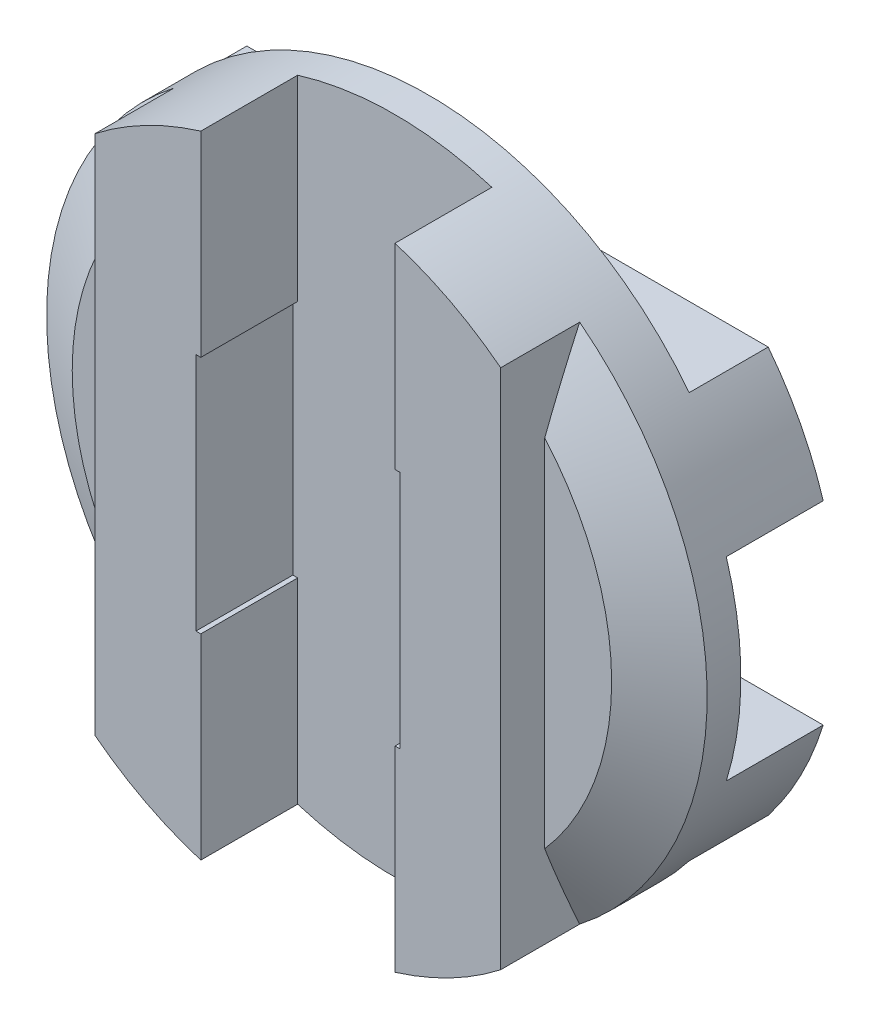
SolidWorks part; units mm, degrees
ref_plane "Front" through (0, 0, 0) normal (0, 0, 1) x (1, 0, 0)
ref_plane "Top" through (0, 0, 0) normal (0, 1, 0) x (1, 0, 0)
ref_plane "Right" through (0, 0, 0) normal (1, 0, 0) x (0, 0, -1)
sketch "Sketch1" plane through (0, 0, 0) normal (0, 0, 1) x (1, 0, 0)
  circle A0 centre (0, 0) radius 9.525
  point P3 (0, 9.525)
extrude "Boss-Extrude1" add sketch "Sketch1" against normal mid plane 6.0452
sketch "Sketch2" plane through (0, 0, 3.0226) normal (0, 0, 1) x (1, 0, 0)
  line L0 (-2.8004, 9.525) -> (2.8003, -9.525) construction
  line L1 (-2.8004, 9.525) -> (2.8003, 9.525)
  line L2 (-2.8004, 9.525) -> (-2.8003, -9.525)
  line L3 (-2.8003, -9.525) -> (2.8003, -9.525)
  line L4 (2.8003, 9.525) -> (2.8003, -9.525)
  circle A0 centre (0, 0) radius 9.525 construction
extrude "Cut-Extrude1" cut sketch "Sketch2" against normal blind 2.794
sketch "Sketch3" plane through (0, 0, -3.0226) normal (0, 0, -1) x (-1, 0, 0)
  line L1 (-9.525, 2.8004) -> (9.525, 2.8004)
  line L2 (-9.525, 2.8004) -> (-9.525, -2.8003)
  line L3 (-9.525, -2.8003) -> (9.525, -2.8003)
  line L4 (9.525, 2.8004) -> (9.525, -2.8003)
  line L14 (2.8004, 9.525) -> (-2.8003, 9.525) construction
  line L15 (9.525, 2.8004) -> (-9.525, -2.8003) construction
  circle A0 centre (0, 0) radius 9.525 construction
extrude "Cut-Extrude2" cut sketch "Sketch3" against normal blind 2.794
sketch "Sketch4" plane through (0, 0, 3.0226) normal (0, 0, 1) x (1, 0, 0)
  line L0 (-2.8004, 0) -> (-5.8484, 0) construction
  line L1 (9.525, 9.525) -> (5.8484, 9.525)
  line L2 (9.525, 9.525) -> (9.525, -9.525)
  line L3 (9.525, -9.525) -> (5.8484, -9.525)
  line L4 (5.8484, 9.525) -> (5.8484, -9.525)
  line L5 (-9.525, 9.525) -> (-5.8484, 9.525)
  line L6 (-9.525, 9.525) -> (-9.525, -9.525)
  line L7 (-9.525, -9.525) -> (-5.8483, -9.525)
  line L8 (-5.8484, 9.525) -> (-5.8483, -9.525)
  line L9 (-2.8004, 9.104) -> (-2.8004, -9.104) construction
  line L10 (2.8003, 0) -> (5.8484, 0) construction
  line L11 (2.8003, -9.104) -> (2.8003, 9.104) construction
  line L12 (-2.8004, 9.525) -> (2.8003, 9.525) construction
  line L13 (-2.8003, -9.525) -> (2.8003, -9.525) construction
  line L14 (2.8003, 9.525) -> (2.8003, -9.525) construction
  circle A1 centre (0, 0) radius 9.525 construction
extrude "Cut-Extrude3" cut sketch "Sketch4" against normal blind 1.27
sketch "Sketch5" plane through (0, 0, -3.0226) normal (0, 0, -1) x (-1, 0, 0)
  line L0 (-9.525, 9.525) -> (-5.8484, 9.525) construction
  line L1 (-9.525, 9.525) -> (9.525, 9.525)
  line L2 (-9.525, 9.525) -> (-9.525, 5.8484)
  line L3 (-9.525, 5.8484) -> (9.525, 5.8484)
  line L4 (9.525, 9.525) -> (9.525, 5.8484)
  line L5 (9.525, -9.525) -> (-9.525, -9.525)
  line L6 (9.525, -9.525) -> (9.525, -5.8483)
  line L7 (9.525, -5.8483) -> (-9.525, -5.8483)
  line L8 (-9.525, -9.525) -> (-9.525, -5.8483)
  line L9 (0, 2.8004) -> (0, 5.8484) construction
  line L10 (-9.104, 2.8004) -> (9.104, 2.8004) construction
  line L11 (-9.525, 2.8004) -> (-9.525, -2.8003) construction
  line L12 (0, -5.8483) -> (0, -2.8003) construction
  line L13 (-9.104, -2.8003) -> (9.104, -2.8003) construction
  circle A0 centre (0, 0) radius 9.525 construction
extrude "Cut-Extrude4" cut sketch "Sketch5" against normal blind 1.27
chamfer "Chamfer1" distance 1.7464 angle 30 4 edges at (0, -9.525, -1.7526) (0, 9.525, -1.7526) (-9.525, 0, 1.7526) (9.525, 0, 1.7526)
sketch "Sketch6" plane through (0, 0, 3.0226) normal (0, 0, 1) x (1, 0, 0)
  line L0 (-2.9404, 3.4528) -> (2.9404, -3.4528) construction
  line L1 (-2.9404, 3.4528) -> (2.9404, 3.4528)
  line L2 (-2.9404, 3.4528) -> (-2.9404, -3.4528)
  line L3 (-2.9404, -3.4528) -> (2.9404, -3.4528)
  line L4 (2.9404, 3.4528) -> (2.9404, -3.4528)
  dimension "D1" = 5.8807
  dimension "D2" = 6.9056
extrude "Cut-Extrude5" cut sketch "Sketch6" against normal up to surface (2.794 mm away) up to face at (0, 0, 0.2286)
sketch "Sketch7" plane through (0, 0, -3.0226) normal (0, 0, -1) x (-1, 0, 0)
  line L0 (-3.4528, 2.9404) -> (3.4528, -2.9404) construction
  line L1 (-3.4528, 2.9404) -> (3.4528, 2.9404)
  line L2 (-3.4528, 2.9404) -> (-3.4528, -2.9404)
  line L3 (-3.4528, -2.9404) -> (3.4528, -2.9404)
  line L4 (3.4528, 2.9404) -> (3.4528, -2.9404)
  line L5 (2.9404, 3.4528) -> (2.9404, -3.4528) construction
  line L6 (2.9404, 3.4528) -> (-2.9404, 3.4528) construction
extrude "Cut-Extrude6" cut sketch "Sketch7" against normal up to surface (2.794 mm away) up to face at (0, 0, -0.2286)
sketch "Sketch8" plane through (0, 0, 0) normal (1, 0, 0) x (0, 0, -1)
  line L0 (-3.0226, 9.104) -> (-3.0226, 3.4528) construction
  line L2 (3.0226, 2.8004) -> (3.0226, 5.8484) construction
  point P0 (3.0226, 9.525)
  point P1 (-3.0226, 9.525)
equation "\"D1@Cut-Extrude2\" = \"Tooth depth@Cut-Extrude1\""
equation "\"D1@Cut-Extrude4\" = \"Tooth depth 2@Cut-Extrude3\""
equation "\"D1@Chamfer1\" = \"D1@Sketch4\" * .475"
equation "\"D1@Sketch6\" = \"Tooth gap@Sketch2\" * 1.05"
equation "\"D2@Sketch6\" = \"OD@Sketch1\" * .3625"
